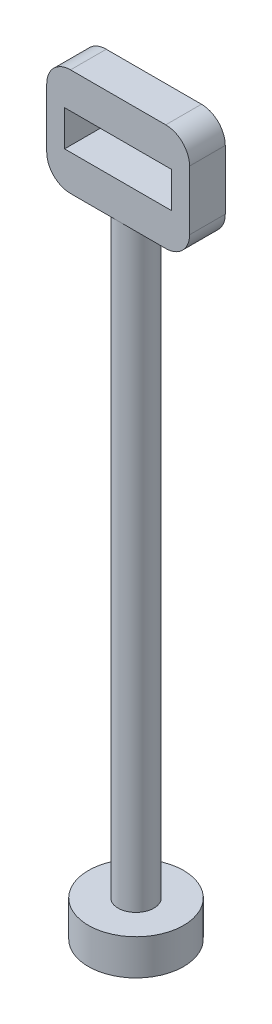
SolidWorks part; units mm, degrees
ref_plane "Front Plane" through (0, 0, 0) normal (0, 0, 1) x (1, 0, 0)
ref_plane "Top Plane" through (0, 0, 0) normal (0, 1, 0) x (1, 0, 0)
ref_plane "Right Plane" through (0, 0, 0) normal (1, 0, 0) x (0, 0, -1)
sketch "Sketch1" plane through (0, 0, 0) normal (0, 1, 0) x (1, 0, 0)
  circle A0 centre (0, 0) radius 1.5
extrude "Boss-Extrude1" add sketch "Sketch1" along normal blind 50
sketch "Sketch2" plane through (0, 0, 0) normal (0, -1, 0) x (-1, 0, 0)
  circle A0 centre (0, 0) radius 4
extrude "Boss-Extrude2" add sketch "Sketch2" along normal blind 3
ref_plane "Plane1" through (0, 0, 1.5) normal (0, 0, 1) x (1, 0, 0)
sketch "Sketch4" plane through (0, 0, 1.5) normal (0, 0, 1) x (1, 0, 0)
  line L0 (0, 50) -> (6, 50)
  line L1 (1.5, 50) -> (-1.5, 50) construction
  line L2 (0, 50) -> (-6, 50)
  line L3 (-6, 50) -> (-6, 59)
  line L4 (-6, 59) -> (6, 59)
  line L5 (6, 59) -> (6, 50)
extrude "Boss-Extrude3" add sketch "Sketch4" against normal blind 3
sketch "Sketch5" plane through (0, 0, 1.5) normal (0, 0, 1) x (1, 0, 0)
  line L0 (0, 50) -> (0, 53)
  line L1 (0, 59) -> (0, 56)
  line L2 (6, 59) -> (-6, 59) construction
  line L3 (0, 56) -> (0, 53)
  line L5 (4.5, 56) -> (-4.5, 56)
  line L6 (4.5, 56) -> (4.5, 53)
  line L7 (4.5, 53) -> (-4.5, 53)
  line L8 (-4.5, 56) -> (-4.5, 53)
  line L9 (4.5, 56) -> (-4.5, 53) construction
  line L10 (4.5, 53) -> (-4.5, 56) construction
  point P8 (0, 54.5)
extrude "Cut-Extrude1" cut sketch "Sketch5" against normal blind 4 contours L5 L8 L7 L3 | L7 L6 L5 L3
fillet "Fillet1" radius 2 4 edges at (-6, 59, 0) (6, 59, 0) (6, 50, 0) (-6, 50, 0)
